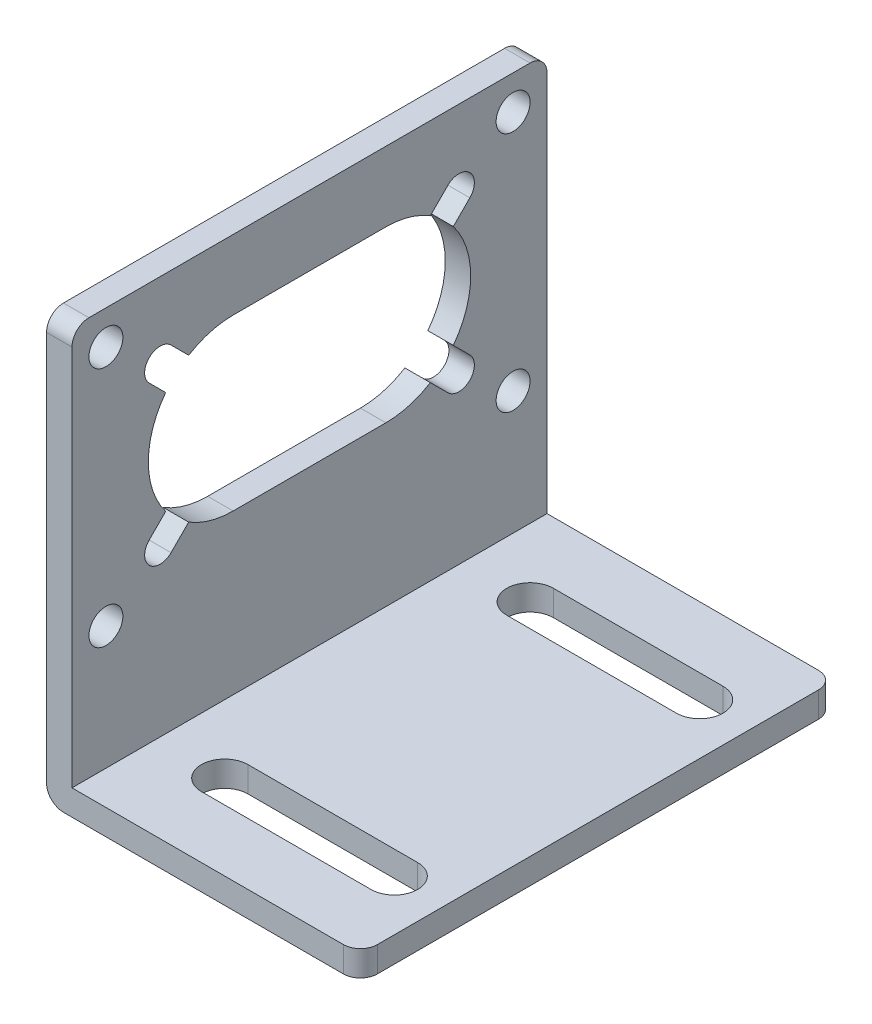
SolidWorks part; units mm, degrees
ref_plane "前视基准面" through (0, 0, 0) normal (0, 0, 1) x (1, 0, 0)
ref_plane "上视基准面" through (0, 0, 0) normal (0, 1, 0) x (1, 0, 0)
ref_plane "右视基准面" through (0, 0, 0) normal (1, 0, 0) x (0, 0, -1)
sketch "草图1" plane through (0, 0, 0) normal (0, 0, 1) x (1, 0, 0)
  line L0 (0, 0) -> (37, 0)
  line L1 (37, 0) -> (37, 3)
  line L2 (37, 3) -> (3, 3)
  line L6 (0, 0) -> (0, 50)
  line L8 (3, 3) -> (3, 50)
  line L9 (3, 50) -> (0, 50)
  dimension "D1" = 50
  dimension "D2" = 37
  dimension "D3" = 3
  dimension "D4" = 3
extrude "凸台-拉伸1" add sketch "草图1" along normal blind 56
sketch "草图2" plane through (0, 3, 0) normal (0, 1, 0) x (1, 0, 0)
  line L0 (11, -10) -> (31, -10) construction
  line L1 (11, -7.25) -> (31, -7.25)
  line L2 (11, -12.75) -> (31, -12.75)
  line L4 (0, -56) -> (0, 0) construction
  line L8 (11, -46) -> (31, -46) construction
  line L9 (11, -48.75) -> (31, -48.75)
  line L10 (11, -43.25) -> (31, -43.25)
  arc A0 (11, -7.25) -> (11, -12.75) centre (11, -10) ccw
  arc A1 (31, -12.75) -> (31, -7.25) centre (31, -10) ccw
  arc A2 (11, -48.75) -> (11, -43.25) centre (11, -46) cw
  arc A3 (31, -43.25) -> (31, -48.75) centre (31, -46) cw
  point P2 (21, -10)
  point P16 (21, -46)
  dimension "D1" = 20
  dimension "D2" = 11
  dimension "D3" = 5.5
  dimension "D5" = 36
extrude "切除-拉伸1" cut sketch "草图2" against normal blind 56 contours L2 A1 L1 A0 | L10 A3 L9 A2
sketch "草图3" plane through (3, 0, 0) normal (1, 0, 0) x (0, 0, -1)
  line L0 (-37, 31.7667) -> (-19, 31.7667) construction
  line L1 (-37, 41.7667) -> (-19, 41.7667)
  line L2 (-37, 21.7667) -> (-19, 21.7667)
  line L3 (-9.099, 23.75) -> (-11.0498, 25.7008)
  line L4 (0, 3) -> (0, 50) construction
  line L5 (-56, 50) -> (0, 50) construction
  line L8 (-9.099, 39.7835) -> (-11.0498, 37.8326)
  line L9 (-56, 3) -> (-56, 50) construction
  line L10 (-11.6787, 42.3631) -> (-13.7587, 40.2831)
  line L11 (-11.6787, 21.1703) -> (-13.7587, 23.2504)
  line L13 (-46.901, 39.7835) -> (-44.9502, 37.8326)
  line L14 (-44.3213, 21.1703) -> (-42.2413, 23.2504)
  line L15 (-46.901, 23.75) -> (-44.9502, 25.7008)
  line L16 (-44.3213, 42.3631) -> (-42.2413, 40.2831)
  arc A0 (-37, 41.7667) -> (-42.2413, 40.2831) centre (-37, 31.7667) ccw
  arc A1 (-19, 21.7667) -> (-13.7587, 23.2504) centre (-19, 31.7667) ccw
  circle A2 centre (-52, 46) radius 2
  circle A5 centre (-4, 46) radius 2
  arc A6 (-9.099, 39.7835) -> (-11.6787, 42.3631) centre (-10.3888, 41.0733) ccw
  arc A8 (-13.7587, 40.2831) -> (-19, 41.7667) centre (-19, 31.7667) ccw
  arc A9 (-9.099, 23.75) -> (-11.6787, 21.1703) centre (-10.3888, 22.4602) cw
  arc A10 (-46.901, 23.75) -> (-44.3213, 21.1703) centre (-45.6112, 22.4602) ccw
  arc A11 (-46.901, 39.7835) -> (-44.3213, 42.3631) centre (-45.6112, 41.0733) cw
  arc A12 (-44.9502, 37.8326) -> (-44.9502, 25.7008) centre (-37, 31.7667) ccw
  arc A13 (-42.2413, 23.2504) -> (-37, 21.7667) centre (-37, 31.7667) ccw
  arc A14 (-11.0498, 25.7008) -> (-11.0498, 37.8326) centre (-19, 31.7667) ccw
  circle A15 centre (-4, 17.5335) radius 2
  circle A16 centre (-52, 17.5335) radius 2
  point P2 (-28, 31.7667)
  point P19 (-12.8197, 38.6425)
  dimension "D3" = 4
  dimension "D5" = 4
  dimension "D1" = 20
  dimension "D6" = 4
  dimension "D7" = 28
extrude "切除-拉伸2" cut sketch "草图3" against normal through all
fillet "圆角1" radius 2 5 edges at (37, 1.5, 0) (37, 1.5, 56) (0, 0, 28) (1.5, 50, 0) (1.5, 50, 56)
